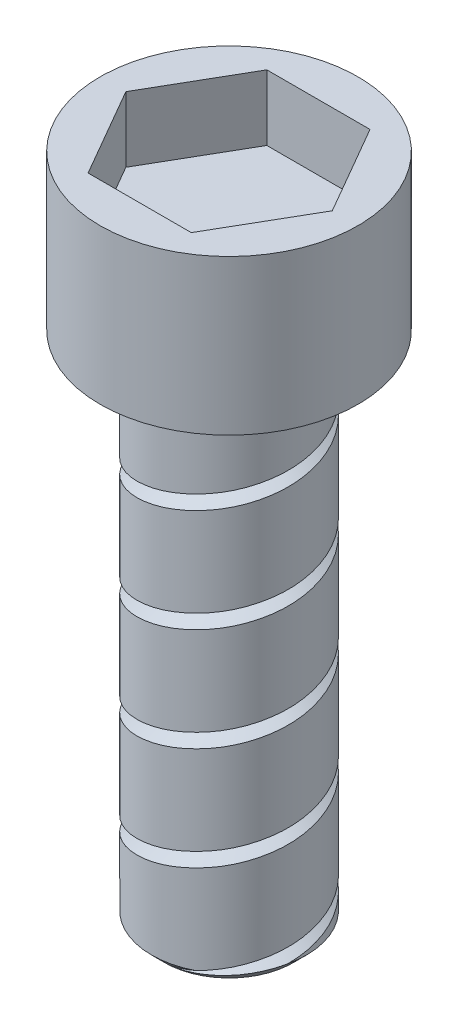
SolidWorks part; units mm, degrees
ref_plane "Front Plane" through (0, 0, 0) normal (0, 0, 1) x (1, 0, 0)
ref_plane "Top Plane" through (0, 0, 0) normal (0, 1, 0) x (1, 0, 0)
ref_plane "Right Plane" through (0, 0, 0) normal (1, 0, 0) x (0, 0, -1)
sketch "Sketch1" plane through (0, 0, 0) normal (0, 1, 0) x (1, 0, 0)
  circle A0 centre (0, 0) radius 1.5
  dimension "D1" = 3
extrude "Boss-Extrude1" add sketch "Sketch1" along normal blind 10
sketch "Sketch2" plane through (0, 10, 0) normal (0, 1, 0) x (-1, 0, 0)
  circle A0 centre (0, 0) radius 2.5
extrude "Boss-Extrude2" add sketch "Sketch2" along normal blind 3
sketch "Sketch3" plane through (0, 13, 0) normal (0, 1, 0) x (1, 0, 0)
  line L1 (2.0005, 0) -> (1.0002, 1.7325)
  line L2 (1.0002, 1.7325) -> (-1.0002, 1.7325)
  line L3 (-1.0002, 1.7325) -> (-2.0005, 0)
  line L4 (-2.0005, 0) -> (-1.0002, -1.7325)
  line L5 (-1.0002, -1.7325) -> (1.0002, -1.7325)
  line L6 (1.0002, -1.7325) -> (2.0005, 0)
  circle A0 centre (0, 0) radius 1.7325 construction
extrude "Cut-Extrude2" cut sketch "Sketch3" against normal blind 1.27
chamfer "Chamfer1" distance 0.254 angle 45 1 edges at (0, 0, 1.5)
sketch "Sketch4" plane through (0, 0, 0) normal (0, -1, 0) x (1, 0, 0)
  circle A0 centre (0, 0) radius 1.2599
curve "Helix/Spiral1" pitch 2 height 9.04 turns 4.52
sketch "Sketch6" plane through (0, 0, 0) normal (1, 0, 0) x (0, 0, -1)
  line L1 (-1.2638, 0) -> (-2.577, 0.5701)
  line L2 (-2.577, 0.5701) -> (-2.4142, -0.8522)
  line L3 (-2.4142, -0.8522) -> (-1.2638, 0)
  circle A0 centre (-2.085, -0.094) radius 0.4133 construction
sweep "Cut-Sweep4" cut profiles "Sketch6" path "Helix/Spiral1"
